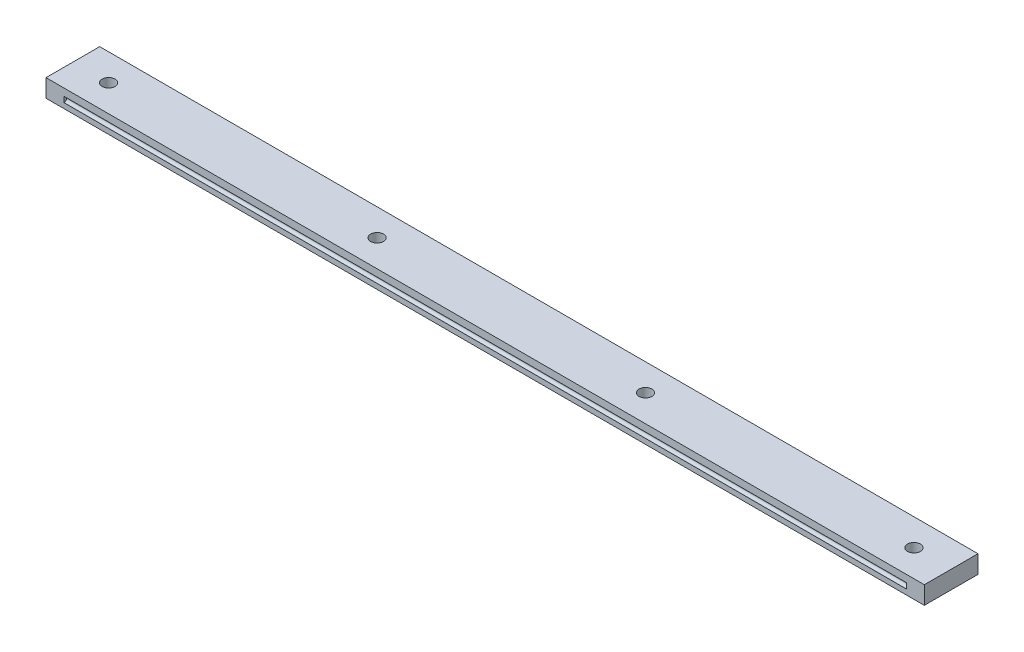
SolidWorks part; units mm, degrees
ref_plane "Front Plane" through (0, 0, 0) normal (0, 0, 1) x (1, 0, 0)
ref_plane "Top Plane" through (0, 0, 0) normal (0, 1, 0) x (1, 0, 0)
ref_plane "Right Plane" through (0, 0, 0) normal (1, 0, 0) x (0, 0, -1)
sketch "Sketch1" plane through (0, 0, 0) normal (0, 0, 1) x (1, 0, 0)
  line L1 (0, 0) -> (245.4, 0)
  line L2 (0, 0) -> (0, 5)
  line L3 (0, 5) -> (245.4, 5)
  line L4 (245.4, 0) -> (245.4, 5)
  dimension "D1" = 5
  dimension "D2" = 245.4
extrude "Main_Body" add sketch "Sketch1" along normal blind 15
sketch "Sketch3" plane through (0, 0, 0) normal (0, -1, 0) x (1, 0, 0)
  line L0 (0, 7.5) -> (10, 7.5) construction
  line L1 (0, 15) -> (0, 0) construction
  circle A0 centre (10, 7.5) radius 1.8
  circle A1 centre (85, 7.5) radius 1.8
  circle A2 centre (160, 7.5) radius 1.8
  circle A3 centre (235, 7.5) radius 1.8
  dimension "D1" = 3.6
  dimension "D2" = 10
  dimension "D3" = 4
extrude "Screw_Holes" cut sketch "Sketch3" against normal blind 5
sketch "Sketch4" plane through (0, 0, 0) normal (0, -1, 0) x (1, 0, 0)
  circle A0 centre (10, 7.5) radius 3
  circle A1 centre (85, 7.5) radius 3
  circle A2 centre (160, 7.5) radius 3
  circle A3 centre (235, 7.5) radius 3
  dimension "D1" = 6
  dimension "D2" = 4
extrude "Screw_Head_Holes" cut sketch "Sketch4" against normal blind 2
sketch "Sketch2" plane through (0, 0, 15) normal (0, 0, 1) x (1, 0, 0)
  line L0 (0, 5) -> (0, 0) construction
  line L1 (5, 3) -> (240.4, 3)
  line L2 (5, 3) -> (5, 1.45)
  line L3 (5, 1.45) -> (240.4, 1.45)
  line L4 (240.4, 3) -> (240.4, 1.45)
  line L5 (245.4, 0) -> (245.4, 5) construction
  line L6 (245.4, 5) -> (0, 5) construction
  dimension "D1" = 5
  dimension "D2" = 1.55
  dimension "D3" = 5
  dimension "D4" = 2
extrude "Channel_A" cut sketch "Sketch2" against normal blind 0.75
fillet "Channel_A_Round" radius 0.7 2 edges at (122.7, 1.45, 14.25) (122.7, 3, 14.25)
